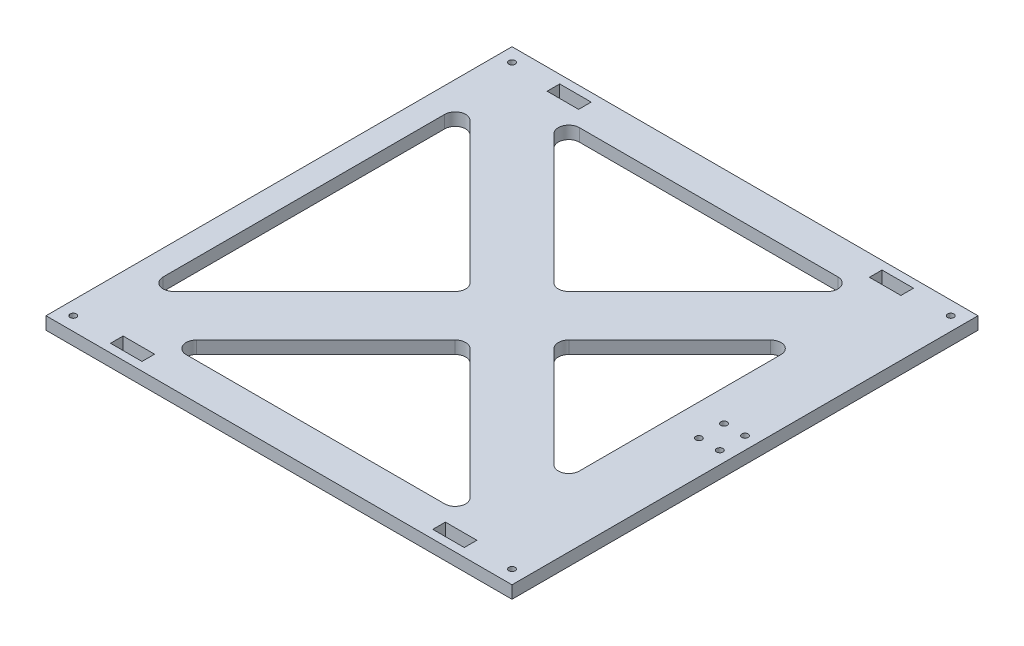
SolidWorks part; units mm, degrees
ref_plane "Спереди" through (0, 0, 0) normal (0, 0, 1) x (1, 0, 0)
ref_plane "Сверху" through (0, 0, 0) normal (0, 1, 0) x (1, 0, 0)
ref_plane "Справа" through (0, 0, 0) normal (1, 0, 0) x (0, 0, -1)
sketch "Эскиз1" plane through (0, 0, 0) normal (0, 1, 0) x (1, 0, 0)
  line L0 (210.5882, 1.4676) -> (-138.0899, 1.4676) construction
  line L1 (-102.7681, -104.5324) -> (-102.7681, -92.1925)
  line L2 (-97.7681, 112.4676) -> (114.2319, 112.4676)
  line L3 (119.2319, 107.4676) -> (119.2319, -104.5324)
  line L4 (-76.0395, 108.4677) -> (-61.0396, 108.4677)
  line L5 (-76.0395, 108.4677) -> (-76.0395, 102.4676)
  line L6 (-76.0395, 102.4676) -> (-61.0396, 102.4676)
  line L7 (-61.0396, 108.4677) -> (-61.0396, 102.4676)
  line L16 (-61.0396, -105.5325) -> (-61.0396, -99.5324)
  line L17 (-76.0395, -99.5324) -> (-61.0396, -99.5324)
  line L18 (-76.0395, -105.5325) -> (-76.0395, -99.5324)
  line L19 (-76.0395, -105.5325) -> (-61.0396, -105.5325)
  line L20 (-97.7681, -109.5324) -> (114.2319, -109.5324)
  line L21 (-102.7681, 112.4676) -> (119.2319, -109.5324) construction
  line L22 (-102.7681, -109.5324) -> (119.2319, 112.4676) construction
  line L23 (8.2319, 1.4676) -> (8.2319, 124.5614) construction
  line L24 (-15.3036, 5.0031) -> (-63.3366, 53.0361)
  line L26 (31.7674, 5.0031) -> (79.8004, 53.0361)
  line L27 (88.336, 49.5006) -> (88.336, -46.5654)
  line L28 (4.6964, 25.0031) -> (-43.3366, 73.0361)
  line L30 (59.8004, 73.0361) -> (11.7674, 25.0031)
  line L31 (31.7674, -2.068) -> (79.8004, -50.101)
  line L35 (-15.3036, -2.068) -> (-63.3366, -50.101)
  line L36 (113.2319, 1.4676) -> (113.2319, 54.2202) construction
  line L37 (103.2319, 1.4676) -> (103.2319, 54.2202) construction
  line L38 (138.7043, 7.4676) -> (96.3994, 7.4676) construction
  line L41 (-63.3366, 53.0361) -> (-102.7681, 92.4676) construction
  line L42 (79.8004, 53.0361) -> (119.2319, 92.8533) construction
  line L44 (-102.7681, 95.1276) -> (-102.7681, 107.4676)
  line L49 (-102.7681, 85.1276) -> (-102.7681, -82.1925)
  line L50 (-102.7681, -104.5324) -> (-102.7681, -109.5324)
  line L51 (-102.7681, -109.5324) -> (-97.7681, -109.5324)
  line L52 (114.2319, -109.5324) -> (119.2319, -109.5324)
  line L53 (119.2319, -109.5324) -> (119.2319, -104.5324)
  line L54 (114.2319, 112.4676) -> (119.2319, 112.4676)
  line L55 (119.2319, 112.4676) -> (119.2319, 107.4676)
  line L56 (-97.7681, 112.4676) -> (-102.7681, 112.4676)
  line L57 (-102.7681, 112.4676) -> (-102.7681, 107.4676)
  line L58 (-63.3366, -50.101) -> (-126.3224, -113.0867) construction
  line L59 (-63.3366, -50.101) -> (172.8399, 186.0756) construction
  line L60 (-43.3366, -70.101) -> (-110.4331, -137.1974) construction
  line L61 (119.2319, 92.8533) -> (195.3067, 169.6724) construction
  line L62 (-43.3366, 73.0361) -> (-126.3224, 156.0219) construction
  line L63 (79.8004, -50.101) -> (154.4882, -124.7887) construction
  line L64 (59.8004, -70.101) -> (131.7703, -142.0708) construction
  line L65 (59.8004, 73.0361) -> (73.3564, 86.5921)
  line L66 (69.8209, 95.1276) -> (-53.3571, 95.1276)
  line L67 (-56.8926, 86.5921) -> (-43.3366, 73.0361)
  line L68 (69.8209, -92.1925) -> (-53.3571, -92.1925)
  line L69 (59.8004, -70.101) -> (73.3564, -83.6569)
  line L70 (59.8004, -70.101) -> (11.7674, -22.068)
  line L71 (4.6964, -22.068) -> (-43.3366, -70.101)
  line L72 (-56.8926, -83.6569) -> (-43.3366, -70.101)
  line L73 (-63.3366, 53.0361) -> (-82.3449, 72.0444)
  line L74 (-90.8805, 68.5088) -> (-90.8805, -65.5737)
  line L75 (-82.3449, -69.1093) -> (-63.3366, -50.101)
  line L76 (92.5033, -105.5325) -> (77.5034, -105.5325)
  line L77 (77.5034, -105.5325) -> (77.5034, -99.5324)
  line L78 (92.5033, -99.5324) -> (77.5034, -99.5324)
  line L79 (92.5033, -105.5325) -> (92.5033, -99.5324)
  line L80 (92.5033, 108.4677) -> (92.5033, 102.4676)
  line L81 (92.5033, 102.4676) -> (77.5034, 102.4676)
  line L82 (77.5034, 108.4677) -> (77.5034, 102.4676)
  line L83 (92.5033, 108.4677) -> (77.5034, 108.4677)
  line L84 (-108.7681, 133.1003) -> (-108.7681, -149.0407) construction
  line L91 (-102.7681, -82.1925) -> (-102.7681, -92.1925)
  line L92 (-102.7681, 95.1276) -> (-102.7681, 85.1276)
  circle A0 centre (-96.2681, 105.9676) radius 1.5
  circle A1 centre (112.7319, 105.9676) radius 1.5
  circle A2 centre (-96.2681, -103.0324) radius 1.5
  circle A4 centre (112.7319, -103.0324) radius 1.5
  arc A5 (79.8004, 53.0361) -> (88.336, 49.5006) centre (83.336, 49.5006) cw
  arc A6 (4.6964, 25.0031) -> (11.7674, 25.0031) centre (8.2319, 28.5386) ccw
  arc A10 (79.8004, -50.101) -> (88.336, -46.5654) centre (83.336, -46.5654) ccw
  arc A15 (31.7674, 5.0031) -> (31.7674, -2.068) centre (35.303, 1.4676) ccw
  arc A16 (-15.3036, 5.0031) -> (-15.3036, -2.068) centre (-18.8392, 1.4676) cw
  circle A17 centre (103.2319, 7.4676) radius 1.5
  circle A18 centre (113.2319, 7.4676) radius 1.5
  circle A19 centre (113.2319, -4.5324) radius 1.5
  circle A20 centre (103.2319, -4.5324) radius 1.5
  arc A25 (73.3564, 86.5921) -> (69.8209, 95.1276) centre (69.8209, 90.1276) ccw
  arc A26 (-53.3571, 95.1276) -> (-56.8926, 86.5921) centre (-53.3571, 90.1276) ccw
  arc A27 (4.6964, -22.068) -> (11.7674, -22.068) centre (8.2319, -25.6035) cw
  arc A28 (73.3564, -83.6569) -> (69.8209, -92.1925) centre (69.8209, -87.1925) cw
  arc A29 (-53.3571, -92.1925) -> (-56.8926, -83.6569) centre (-53.3571, -87.1925) cw
  arc A30 (-90.8805, -65.5737) -> (-82.3449, -69.1093) centre (-85.8805, -65.5737) ccw
  arc A31 (-82.3449, 72.0444) -> (-90.8805, 68.5088) centre (-85.8805, 68.5088) ccw
  point P25 (119.2319, 1.4676)
  point P26 (-102.7681, 1.4676)
  point P45 (88.336, 61.5716)
  point P48 (8.2319, 21.4676)
  point P53 (-51.8722, 81.5716)
  point P56 (-71.8722, 61.5716)
  point P58 (88.336, 1.4676)
  point P60 (81.8919, 95.1276)
  point P64 (-65.4281, 95.1276)
  point P72 (-71.8722, 1.4676)
  point P74 (28.2319, 1.4676)
  point P77 (-11.7681, 1.4676)
  point P95 (-90.8805, 1.4676)
  point P117 (-90.8805, -77.6448)
  point P120 (-90.8805, 80.5799)
  dimension "D3" = 3
  dimension "D4" = 3
  dimension "D5" = 104.5
  dimension "D7" = 3
  dimension "D8" = 3
  dimension "D13" = 5
  dimension "D14" = 5
  dimension "D18" = 3
  dimension "D19" = 3
  dimension "D22" = 104.5
  dimension "D24" = 5
  dimension "D25" = 5
  dimension "D1" = 222
  dimension "D2" = 111
  dimension "D6" = 104.5
  dimension "D9" = 20
  dimension "D10" = 20
  dimension "D11" = 6
  dimension "D15" = 6
  dimension "D16" = 10
  dimension "D17" = 6
  dimension "D20" = 101
  dimension "D23" = 104.5
extrude "Бобышка-Вытянуть1" add sketch "Эскиз1" along normal blind 6
